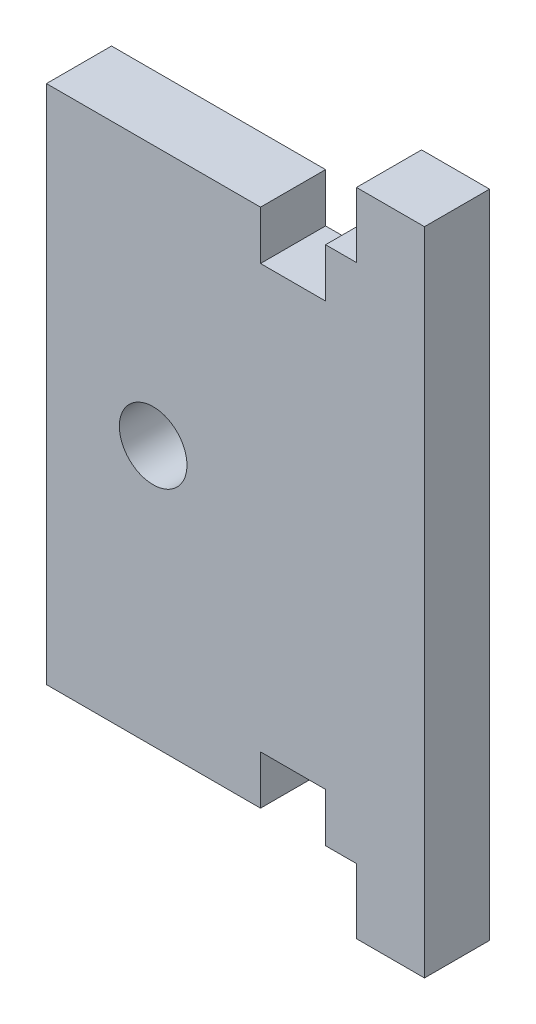
SolidWorks part; units mm, degrees
material "AISI 4130 Steel, annealed at 865C"
ref_plane "X-Y Datum" through (0, 0, 0) normal (0, 0, 1) x (1, 0, 0)
ref_plane "X-Z Datum" through (0, 0, 0) normal (0, 1, 0) x (1, 0, 0)
ref_plane "Y-Z Datum" through (0, 0, 0) normal (1, 0, 0) x (0, 0, -1)
sketch "Sketch2" plane through (0, 0, 0) normal (0, 0, 1) x (1, 0, 0)
  line L0 (34.925, 127) -> (0, 127) construction
  line L1 (0, 0) -> (43.942, 0)
  line L2 (0, 0) -> (0, 127)
  line L3 (0, 127) -> (43.942, 127)
  line L4 (43.942, 0) -> (43.942, 127)
  point P7 (17.4625, 31.75)
  point P8 (17.4625, 95.25)
  dimension "D1" = 43.942
extrude "Boss-Extrude1" add sketch "Sketch2" along normal blind 6.35
hole_wizard "M6 Clearance Hole1" positions "Sketch3" profile "Sketch4" hole size "M6" standard "ANSI Metric" end condition through all
sketch "Sketch3" plane through (0, 0, 6.35) normal (0, 0, 1) x (1, 0, 0)
  point P0 (17.4625, 31.75)
  point P3 (17.4625, 95.25)
sketch "Sketch4" plane through (17.4625, 31.75, 6.35) normal (1, 0, 0) x (0, -1, 0)
  line L0 (0, 0) -> (0, 6.35)
  line L1 (0, 6.35) -> (3.3, 6.35)
  line L2 (3.3, 6.35) -> (3.3, 0)
  line L5 (3.3, 0) -> (0, 0)
  line L11 (0, -6.35) -> (0, 107.95) construction
  dimension "Thru Hole Dia." = 6.6
  dimension "Thru Hole Depth" = 6.35
sketch "Sketch5" plane through (0, 0, 6.35) normal (0, 0, 1) x (1, 0, 0)
  line L0 (7.0505, 127) -> (7.0505, 0)
  line L1 (43.942, 127) -> (0, 127) construction
  line L2 (0, 0) -> (43.942, 0) construction
  circle A0 centre (17.4625, 95.25) radius 3.3 construction
  point P6 (14.1625, 95.25)
  line M4 (0, 127) -> (0, 0)
  line M5 (0, 0) -> (43.942, 0)
  line M7 (43.942, 127) -> (0, 127)
  dimension "D1" = 7.112
extrude "Cut-Extrude1" cut sketch "Sketch5" against normal through all and the other way through all contours L0 M7 M4 M5
sketch "Sketch6" plane through (0, 0, 6.35) normal (0, 0, 1) x (1, 0, 0)
  line L0 (-3.175, 120.65) -> (38.1, 120.65)
  line L1 (38.1, 120.65) -> (38.1, 130.175)
  line L2 (38.1, 130.175) -> (-3.175, 130.175)
  line L3 (-3.175, 130.175) -> (-3.175, 120.65)
  line L4 (0, 123.825) -> (34.925, 123.825)
  line L5 (34.925, 123.825) -> (34.925, 127)
  line L6 (34.925, 127) -> (0, 127)
  line L7 (0, 127) -> (0, 123.825)
  line L8 (0, 123.825) -> (34.925, 123.825)
  line L9 (34.925, 123.825) -> (34.925, 127)
  line L10 (34.925, 127) -> (0, 127)
  line L11 (0, 127) -> (0, 123.825)
  line L12 (0, 60.325) -> (34.925, 60.325)
  line L13 (34.925, 60.325) -> (34.925, 63.5)
  line L14 (34.925, 63.5) -> (0, 63.5)
  line L15 (0, 63.5) -> (0, 60.325)
  line L16 (0, 60.325) -> (34.925, 60.325)
  line L17 (34.925, 60.325) -> (34.925, 63.5)
  line L18 (34.925, 63.5) -> (0, 63.5)
  line L19 (0, 63.5) -> (0, 60.325)
  line L24 (0, 0) -> (34.925, 0)
  line L25 (34.925, 0) -> (34.925, 3.175)
  line L26 (34.925, 3.175) -> (0, 3.175)
  line L27 (0, 3.175) -> (0, 0)
  line L28 (38.1, 66.675) -> (-3.175, 66.675)
  line L29 (-3.175, 66.675) -> (-3.175, 57.15)
  line L30 (-3.175, 57.15) -> (38.1, 57.15)
  line L31 (38.1, 57.15) -> (38.1, 66.675)
  line L32 (38.1, 6.35) -> (-3.175, 6.35)
  line L33 (-3.175, 6.35) -> (-3.175, -3.175)
  line L34 (-3.175, -3.175) -> (38.1, -3.175)
  line L35 (38.1, -3.175) -> (38.1, 6.35)
  line L36 (37.3062, 127) -> (37.3063, 0)
  line L37 (43.942, 127) -> (7.0505, 127) construction
  line L38 (7.0505, 0) -> (43.942, 0) construction
  line M19 (7.0505, 127) -> (7.0505, 0)
  line M20 (7.0505, 0) -> (43.942, 0)
  line M22 (43.942, 127) -> (7.0505, 127)
  dimension "D5" = 2.3813
  dimension "D1" = 0
  dimension "D2" = 0
  dimension "D4" = 3.175
extrude "Cut-Extrude2" cut sketch "Sketch6" against normal through all contours L36 L9 L8 L0 M22 M19 | L8 L9 M22 M19 | L36 L28 L18 L17 L16 L30 M19 | L17 L18 L16 M19 | L36 L32 L26 L25 M19 M20 | L25 L26 M19 M20
sketch "Sketch7" plane through (0, 0, 6.35) normal (0, 0, 1) x (1, 0, 0)
  line L18 (34.29, 120.65) -> (27.94, 120.65)
  line L19 (34.29, 120.65) -> (34.29, 115.8875)
  line L20 (34.29, 115.8875) -> (27.94, 115.8875)
  line L21 (27.94, 120.65) -> (27.94, 115.8875)
  line L22 (34.29, 71.4375) -> (27.94, 71.4375)
  line L23 (34.29, 71.4375) -> (34.29, 66.675)
  line L24 (34.29, 66.675) -> (27.94, 66.675)
  line L25 (27.94, 71.4375) -> (27.94, 66.675)
  line L26 (34.29, 57.15) -> (27.94, 57.15)
  line L27 (34.29, 57.15) -> (34.29, 52.3875)
  line L28 (34.29, 52.3875) -> (27.94, 52.3875)
  line L29 (27.94, 57.15) -> (27.94, 52.3875)
  line L30 (34.29, 11.1125) -> (27.94, 11.1125)
  line L31 (34.29, 11.1125) -> (34.29, 6.35)
  line L32 (34.29, 6.35) -> (27.94, 6.35)
  line L33 (27.94, 11.1125) -> (27.94, 6.35)
extrude "Cut-Extrude3" cut sketch "Sketch7" against normal through all
sketch "Sketch8" plane through (0, 0, 6.35) normal (0, 0, 1) x (1, 0, 0)
  line L0 (34.925, 63.5) -> (43.942, 63.5)
  line L1 (43.942, 0) -> (43.942, 127) construction
  circle M3 centre (17.4625, 95.25) radius 3.3
  line M4 (37.3062, 120.65) -> (34.29, 120.65)
  line M5 (34.29, 120.65) -> (34.29, 115.8875)
  line M6 (34.29, 115.8875) -> (27.94, 115.8875)
  line M7 (27.94, 115.8875) -> (27.94, 120.65)
  line M8 (27.94, 120.65) -> (7.0505, 120.65)
  line M9 (7.0505, 120.65) -> (7.0505, 66.675)
  line M10 (7.0505, 66.675) -> (27.94, 66.675)
  line M11 (27.94, 66.675) -> (27.94, 71.4375)
  line M12 (27.94, 71.4375) -> (34.29, 71.4375)
  line M13 (34.29, 71.4375) -> (34.29, 66.675)
  line M14 (34.29, 66.675) -> (37.3062, 66.675)
  line M15 (37.3062, 66.675) -> (37.3062, 57.15)
  line M29 (43.942, 0) -> (43.942, 127)
  line M30 (43.942, 127) -> (37.3062, 127)
  line M31 (37.3062, 127) -> (37.3062, 120.65)
extrude "Cut-Extrude4" cut sketch "Sketch8" against normal through all and the other way through all contours L0 M15 M29 M30 M31 M4 M5 M6 M7 M8 M9 M10 M11 M12 M13 M14 M3
